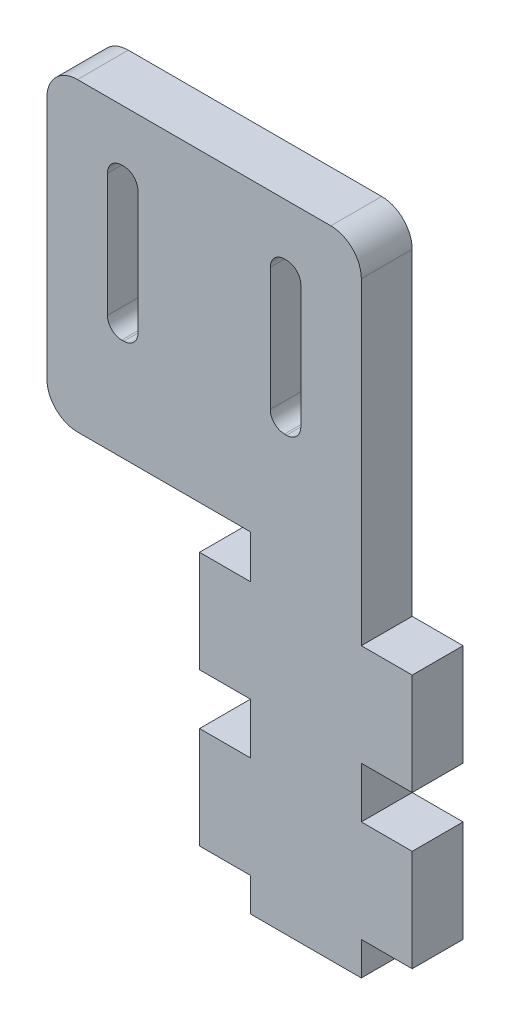
SolidWorks part; units mm, degrees
ref_plane "Front Plane" through (0, 0, 0) normal (0, 0, 1) x (1, 0, 0)
ref_plane "Top Plane" through (0, 0, 0) normal (0, 1, 0) x (1, 0, 0)
ref_plane "Right Plane" through (0, 0, 0) normal (1, 0, 0) x (0, 0, -1)
sketch "Sketch1" plane through (0, 0, 0) normal (0, 0, 1) x (1, 0, 0)
  line L0 (-10.45, -25.7747) -> (-10.45, -35.7747)
  line L1 (5.45, 20.4653) -> (5.45, -10.7747)
  line L2 (10.45, -10.7747) -> (10.45, -20.7747)
  line L3 (-22.45, -6.5347) -> (-5.45, -6.5347)
  line L4 (-10.45, -10.7747) -> (-10.45, -20.7747)
  line L5 (-19.502, 16.9653) -> (-19.502, 4.8653)
  line L6 (-22.45, 23.4653) -> (2.45, 23.4653)
  line L7 (-10.45, -20.7747) -> (-5.45, -20.7747)
  line L8 (0, 28.4653) -> (0, -34.8585) construction
  line L9 (-16.502, 4.8653) -> (-16.502, 16.9653)
  line L10 (-3.498, 16.9653) -> (-3.498, 4.8653)
  line L11 (10.45, -10.7747) -> (5.45, -10.7747)
  line L12 (10.45, -25.7747) -> (5.45, -25.7747)
  line L13 (-10.45, -25.7747) -> (-5.45, -25.7747)
  line L14 (-10.45, -10.7747) -> (-5.45, -10.7747)
  line L15 (-5.45, -6.5347) -> (-5.45, -10.7747)
  line L16 (-0.498, 4.8653) -> (-0.498, 16.9653)
  line L17 (-5.45, -20.7747) -> (-5.45, -25.7747)
  line L18 (5.45, -20.7747) -> (5.45, -25.7747)
  line L19 (10.45, -20.7747) -> (5.45, -20.7747)
  line L20 (10.45, -25.7747) -> (10.45, -35.7747)
  line L21 (5.45, -35.7747) -> (5.45, -39.0585)
  line L22 (-10.45, -35.7747) -> (-5.45, -35.7747)
  line L23 (-25.45, 8.4653) -> (9.447, 8.4653) construction
  line L24 (5.45, -39.0585) -> (-5.45, -39.0585)
  line L25 (-5.45, -35.7747) -> (-5.45, -39.0585)
  line L26 (10.45, -35.7747) -> (5.45, -35.7747)
  line L28 (-2.098, 18.3653) -> (-1.898, 18.3653)
  line L29 (-17.902, 18.3653) -> (-18.102, 18.3653)
  line L30 (-25.45, -3.5347) -> (-25.45, 20.4653)
  line L32 (-17.902, 3.4653) -> (-18.102, 3.4653)
  line L34 (-2.098, 3.4653) -> (-1.898, 3.4653)
  arc A0 (-22.45, 23.4653) -> (-25.45, 20.4653) centre (-22.45, 20.4653) ccw
  arc A1 (2.45, 23.4653) -> (5.45, 20.4653) centre (2.45, 20.4653) cw
  arc A2 (-18.102, 18.3653) -> (-19.502, 16.9653) centre (-18.102, 16.9653) ccw
  arc A3 (-22.45, -6.5347) -> (-25.45, -3.5347) centre (-22.45, -3.5347) cw
  arc A4 (-17.902, 18.3653) -> (-16.502, 16.9653) centre (-17.902, 16.9653) cw
  arc A5 (-18.102, 3.4653) -> (-19.502, 4.8653) centre (-18.102, 4.8653) cw
  arc A6 (-16.502, 4.8653) -> (-17.902, 3.4653) centre (-17.902, 4.8653) cw
  arc A7 (-1.898, 3.4653) -> (-0.498, 4.8653) centre (-1.898, 4.8653) ccw
  arc A8 (-3.498, 4.8653) -> (-2.098, 3.4653) centre (-2.098, 4.8653) ccw
  arc A9 (-1.898, 18.3653) -> (-0.498, 16.9653) centre (-1.898, 16.9653) cw
  arc A10 (-2.098, 18.3653) -> (-3.498, 16.9653) centre (-2.098, 16.9653) ccw
  point P0 (-5, 5)
  point P11 (-25.45, 23.4653)
  point P31 (25.45, 23.4653)
  point P38 (20.45, -6.5347)
  point P41 (-20.45, -6.5347)
  dimension "D1" = 3
  dimension "D2" = 3
  dimension "D3" = 1.4
  dimension "D4" = 3
  dimension "D5" = 1.4
  dimension "D6" = 1.4
  dimension "D7" = 1.4
extrude "Boss-Extrude1" add sketch "Sketch1" along normal blind 5 contours L15 L14 L4 L7 L17 L13 L0 L22 L25 L24 L21 L26 L20 L12 L18 L19 L2 L11 L1 A1 L6 A0 L30 A3 L3 | A6 L32 A5 L5 A2 L29 A4 L9 | A7 L16 A9 L28 A10 L10 A8 L34
